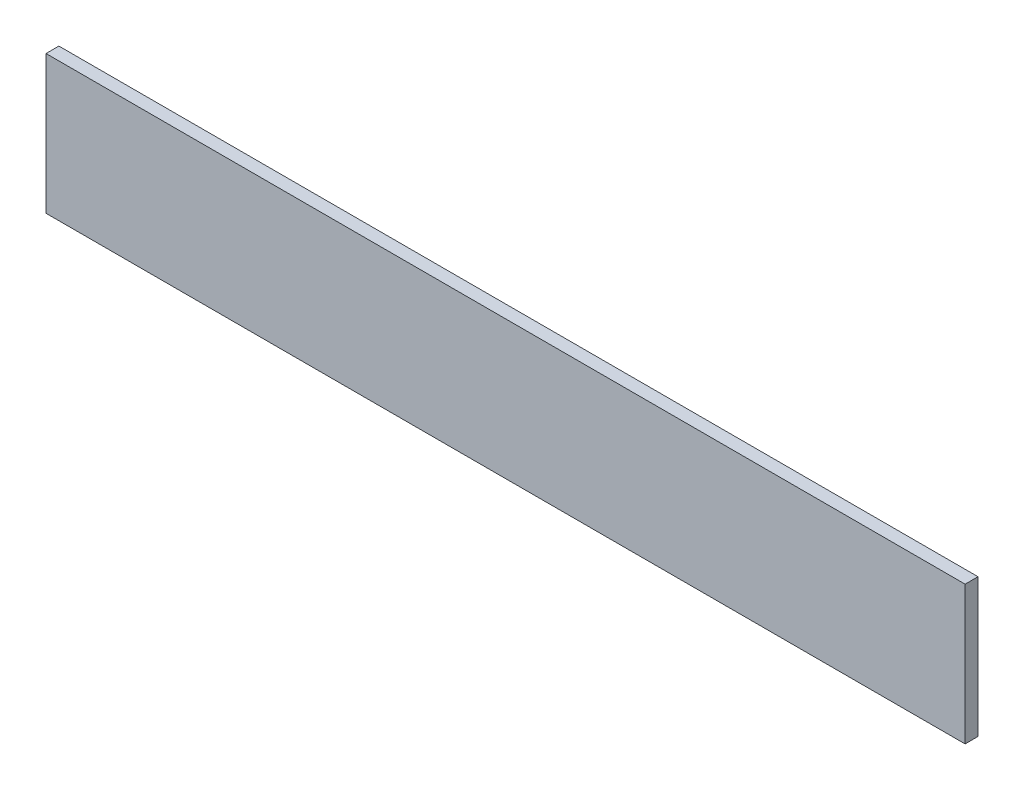
SolidWorks part; units mm, degrees
ref_plane "Plan de face" through (0, 0, 0) normal (0, 0, 1) x (1, 0, 0)
ref_plane "Plan de dessus" through (0, 0, 0) normal (0, 1, 0) x (1, 0, 0)
ref_plane "Plan de droite" through (0, 0, 0) normal (1, 0, 0) x (0, 0, -1)
sketch "Esquisse1" plane through (0, 0, 0) normal (0, 0, 1) x (1, 0, 0)
  line L1 (-204.7706, 126.5596) -> (151.7294, 126.5596)
  line L2 (-204.7706, 126.5596) -> (-204.7706, 72.8796)
  line L3 (-204.7706, 72.8796) -> (151.7294, 72.8796)
  line L4 (151.7294, 126.5596) -> (151.7294, 72.8796)
  dimension "D1" = 356.5
  dimension "D2" = 53.68
extrude "Boss.-Extru.4" add sketch "Esquisse1" along normal blind 5
